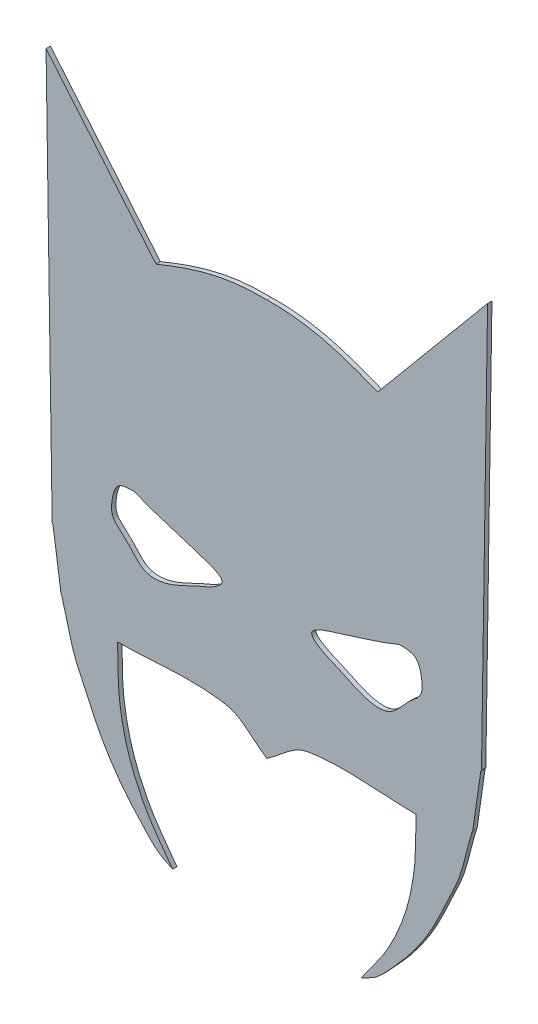
SolidWorks part; units mm, degrees
ref_plane "Ön Düzlem" through (0, 0, 0) normal (0, 0, 1) x (1, 0, 0)
ref_plane "Üst Düzlem" through (0, 0, 0) normal (0, 1, 0) x (1, 0, 0)
ref_plane "Sağ Düzlem" through (0, 0, 0) normal (1, 0, 0) x (0, 0, -1)
sketch "Sketch1" plane through (0, 0, 0) normal (0, 0, 1) x (1, 0, 0)
  line L0 (122.3333, 512) -> (611.6667, 512) construction
  line L2 (486, 734) -> (612, 885)
  line L3 (612, 885) -> (605, 418)
  line L5 (232, 734) -> (106, 885)
  line L6 (106, 885) -> (113, 418)
  spline S0 degree 3 poles (359, 762.0275) (406.0579, 763.2326) (443.1871, 751.5144) (486, 734) knots 2.007023 2.007023 2.007023 2.007023 3 3 3 3
  spline S1 degree 3 poles (605, 418) (604.6667, 417.3333) (604.1133, 416.7367) (604, 416) (600.7744, 395.0335) (598.2256, 373.9665) (595, 353) (594.8867, 352.2633) (594.2192, 351.7124) (594, 351) (587.3333, 329.3333) (584.0086, 306.34) (574, 286) (563.9957, 265.6688) (555.6314, 244.4462) (544, 225) (534.2125, 208.6366) (522.7453, 193.1814) (510, 179) (485.2659, 151.479) (485.8959, 152.448) (467, 143) knots 0 0 0 0 1 1 1 2 2 2 3 3 3 4 4 4 5 5 5 6 6 6 7 7 7 7
  spline S2 degree 3 poles (467, 143) (477.3333, 158) (489.0949, 172.1105) (498, 188) (506.1743, 202.5855) (512.9165, 218.0716) (518, 234) (522.9691, 249.5698) (526.1087, 265.7663) (528, 282) (530.123, 300.2222) (529.3333, 318.6667) (530, 337) knots 0 0 0 0 1 1 1 2 2 2 3 3 3 4 4 4 4
  spline S3 degree 3 poles (530, 337) (488.6667, 337) (446.7116, 344.1424) (406, 337) (387.6935, 333.7883) (374.6667, 317) (359, 307) knots 0 0 0 0 1 1 1 2 2 2 2
  spline S4 degree 3 poles (359, 762.0275) (311.9421, 763.2326) (274.8129, 751.5144) (232, 734) knots 2.007023 2.007023 2.007023 2.007023 3 3 3 3
  spline S5 degree 3 poles (113, 418) (113.3333, 417.3333) (113.8867, 416.7367) (114, 416) (117.2256, 395.0335) (119.7744, 373.9665) (123, 353) (123.1133, 352.2633) (123.7808, 351.7124) (124, 351) (130.6667, 329.3333) (133.9914, 306.34) (144, 286) (154.0043, 265.6688) (162.3686, 244.4462) (174, 225) (183.7875, 208.6366) (195.2547, 193.1814) (208, 179) (232.7341, 151.479) (232.1041, 152.448) (251, 143) knots 0 0 0 0 1 1 1 2 2 2 3 3 3 4 4 4 5 5 5 6 6 6 7 7 7 7
  spline S6 degree 3 poles (251, 143) (240.6667, 158) (228.9051, 172.1105) (220, 188) (211.8257, 202.5855) (205.0835, 218.0716) (200, 234) (195.0309, 249.5698) (191.8913, 265.7663) (190, 282) (187.877, 300.2222) (188.6667, 318.6667) (188, 337) knots 0 0 0 0 1 1 1 2 2 2 3 3 3 4 4 4 4
  spline S7 degree 3 poles (188, 337) (229.3333, 337) (271.2884, 344.1424) (312, 337) (330.3065, 333.7883) (343.3333, 317) (359, 307) knots 0 0 0 0 1 1 1 2 2 2 2
  spline S8 degree 3 poles (495, 422) (476.4348, 417.7806) (455.524, 430.5642) (439, 438) (437.243, 438.7907) (400.4193, 452.0138) (413, 461) (416.6391, 463.5994) (420.7811, 465.5164) (425, 467) (453.5395, 477.0359) (483.1934, 484.0829) (511, 496) knots 5 5 5 5 6 6 6 7 7 7 8 8 8 9 9 9 9
  spline S9 degree 3 poles (511, 496) (519.5752, 495.3875) (528.9101, 496.5431) (533, 487) (534.3709, 483.8013) (535.4279, 480.4328) (536, 477) (537.2415, 469.551) (538.2892, 461.347) (533, 455) (529.5262, 450.8314) (524.9294, 447.7423) (521, 444) (513.5292, 436.8849) (505.7813, 424.4503) (495, 422) knots 0 0 0 0 1 1 1 2 2 2 3 3 3 4 4 4 5 5 5 5
  spline S10 degree 3 poles (207, 496) (198.4248, 495.3875) (189.0899, 496.5431) (185, 487) (183.6291, 483.8013) (182.5721, 480.4328) (182, 477) (180.7585, 469.551) (179.7108, 461.347) (185, 455) (188.4738, 450.8314) (193.0706, 447.7423) (197, 444) (204.4708, 436.8849) (212.2187, 424.4503) (223, 422) knots 0 0 0 0 1 1 1 2 2 2 3 3 3 4 4 4 5 5 5 5
  spline S11 degree 3 poles (223, 422) (241.5652, 417.7806) (262.476, 430.5642) (279, 438) (280.757, 438.7907) (317.5807, 452.0138) (305, 461) (301.3609, 463.5994) (297.2189, 465.5164) (293, 467) (264.4605, 477.0359) (234.8066, 484.0829) (207, 496) knots 5 5 5 5 6 6 6 7 7 7 8 8 8 9 9 9 9
extrude "Boss-Extrude1" add sketch "Sketch1" along normal blind 5
